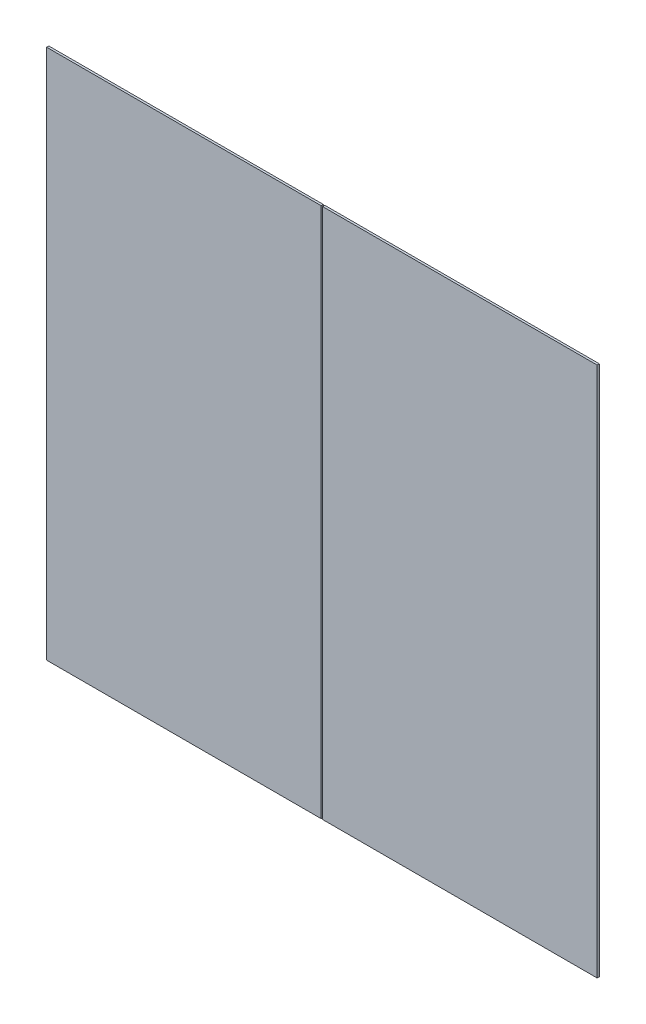
SolidWorks part; units mm, degrees
ref_plane "Front Plane" through (0, 0, 0) normal (0, 0, 1) x (1, 0, 0)
ref_plane "Top Plane" through (0, 0, 0) normal (0, 1, 0) x (1, 0, 0)
ref_plane "Right Plane" through (0, 0, 0) normal (1, 0, 0) x (0, 0, -1)
sketch "Sketch1" plane through (0, 0, 0) normal (0, 0, 1) x (1, 0, 0)
  line L0 (0, 1166.114) -> (0, -1166.114) construction
  line L1 (-1209.04, 1166.114) -> (-3.175, 1166.114)
  line L2 (-1209.04, 1166.114) -> (-1209.04, -1166.114)
  line L3 (-1209.04, -1166.114) -> (-3.175, -1166.114)
  line L4 (1209.04, 1166.114) -> (1209.04, -1166.114)
  line L5 (-3.175, 1166.114) -> (-3.175, -1166.114)
  line L6 (3.175, -1166.114) -> (3.175, 1166.114)
  line L7 (3.175, 1166.114) -> (1209.04, 1166.114)
  line L8 (3.175, -1166.114) -> (1209.04, -1166.114)
  line L9 (-1209.04, 0) -> (1209.04, 0) construction
  dimension "D1" = 2418.08
  dimension "D2" = 2332.228
  dimension "D3" = 6.35
  dimension "D4" = 3.175
extrude "Boss-Extrude1" add sketch "Sketch1" along normal blind 9.525
equation "\"D4@Sketch1\"=\"D3@Sketch1\"/2"
